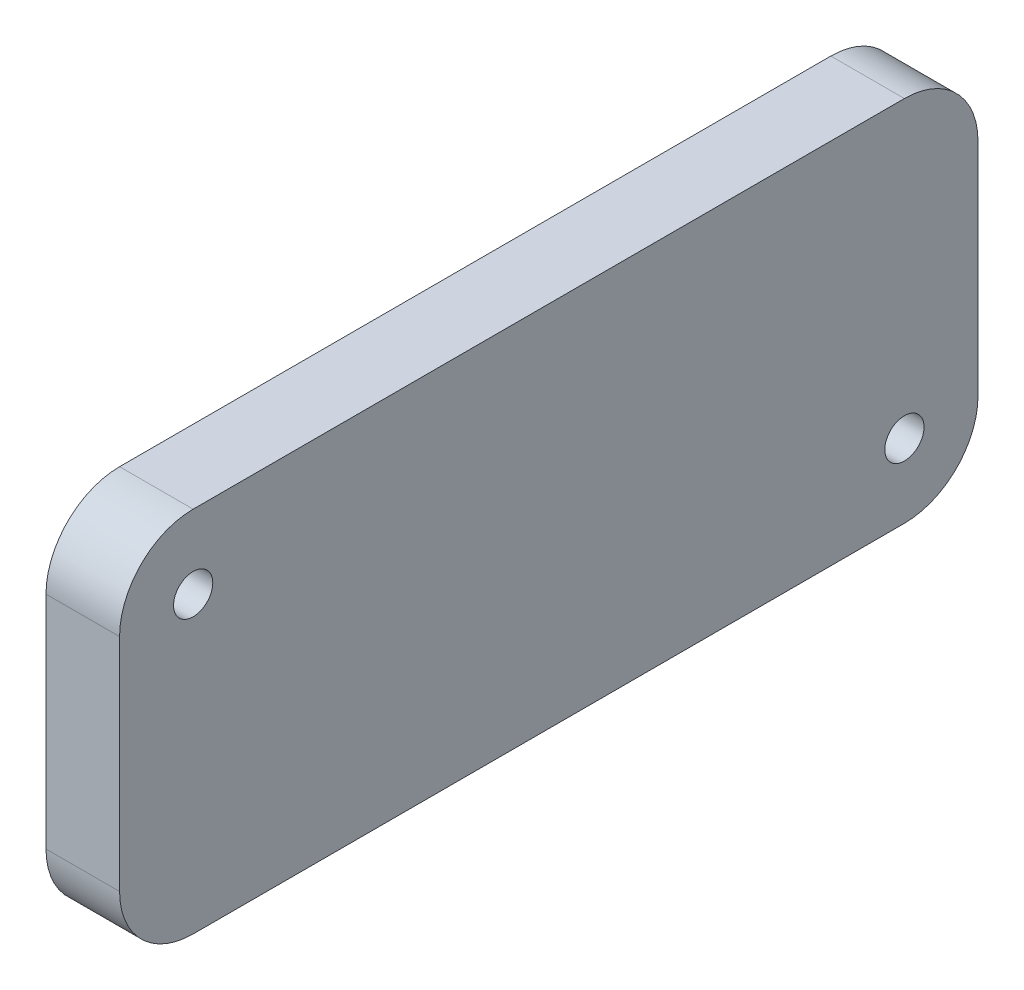
SolidWorks part; units mm, degrees
material "Teca"
ref_plane "Front Plane" through (0, 0, 0) normal (0, 0, 1) x (1, 0, 0)
ref_plane "Top Plane" through (0, 0, 0) normal (0, 1, 0) x (1, 0, 0)
ref_plane "Right Plane" through (0, 0, 0) normal (1, 0, 0) x (0, 0, -1)
sketch "Esboço1" plane through (0, 0, 0) normal (1, 0, 0) x (0, 0, -1)
  line L1 (-17.5, 7.5) -> (17.5, 7.5)
  line L2 (-17.5, 7.5) -> (-17.5, -7.5)
  line L3 (-17.5, -7.5) -> (17.5, -7.5)
  line L4 (17.5, 7.5) -> (17.5, -7.5)
  line L5 (0, -7.5) -> (0, 7.5) construction
  line L6 (-17.5, 0) -> (17.5, 0) construction
  circle A0 centre (-14.5, 4.5) radius 0.8
  circle A1 centre (14.5, -4.5) radius 0.8
  point P0 (0, 0)
  dimension "D3" = 1.6
  dimension "D4" = 1.6
  dimension "D1" = 35
  dimension "D2" = 15
  dimension "D5" = 3
  dimension "D6" = 3
  dimension "D7" = 3
  dimension "D8" = 3
extrude "Ressalto-extrusão1" add sketch "Esboço1" along normal blind 3
fillet "Filete1" radius 3 4 edges at (1.5, -7.5, 17.5) (1.5, 7.5, 17.5) (1.5, 7.5, -17.5) (1.5, -7.5, -17.5)
